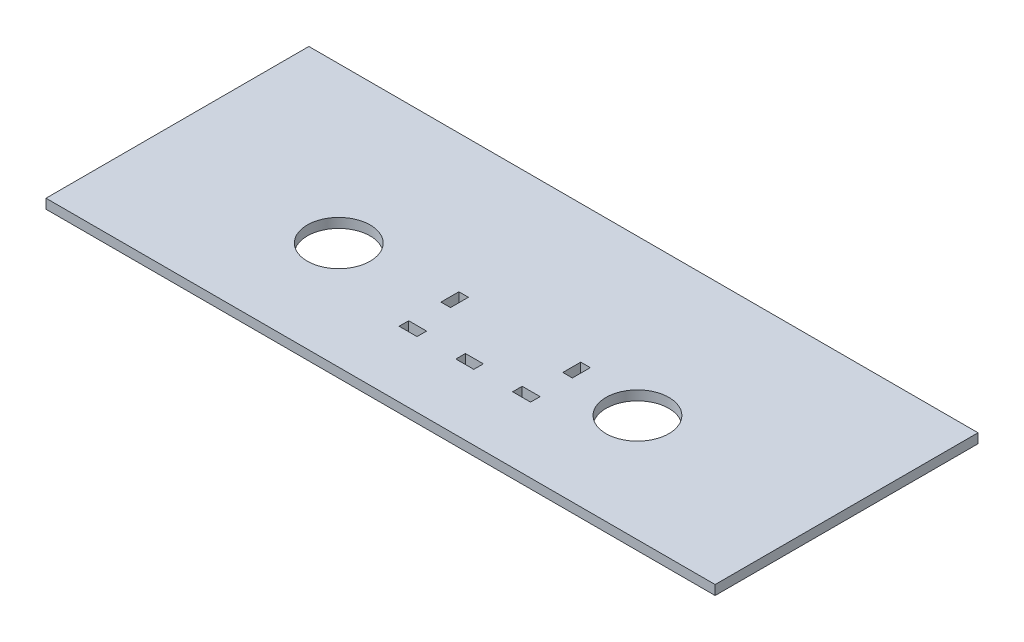
SolidWorks part; units mm, degrees
ref_plane "Front" through (0, 0, 0) normal (0, 0, 1) x (1, 0, 0)
ref_plane "Top" through (0, 0, 0) normal (0, 1, 0) x (1, 0, 0)
ref_plane "Right" through (0, 0, 0) normal (1, 0, 0) x (0, 0, -1)
sketch "Sketch1" plane through (0, 0, 0) normal (0, 1, 0) x (1, 0, 0)
  line L1 (177.8, -69.85) -> (-177.8, -69.85)
  line L2 (177.8, -69.85) -> (177.8, 69.85)
  line L3 (177.8, 69.85) -> (-177.8, 69.85)
  line L4 (-177.8, -69.85) -> (-177.8, 69.85)
  line L5 (177.8, -69.85) -> (-177.8, 69.85) construction
  line L6 (177.8, 69.85) -> (-177.8, -69.85) construction
  point P0 (0, 0)
  dimension "D1" = 355.6
  dimension "D2" = 139.7
extrude "Boss-Extrude1" add sketch "Sketch1" along normal blind 5.08
sketch "Sketch2" plane through (0, 5.08, 0) normal (0, 1, 0) x (1, 0, 0)
  line L0 (-79.375, -12.7) -> (79.375, -12.7)
  line L1 (0, -12.7) -> (0, 0)
  line L2 (177.8, 69.85) -> (-177.8, 69.85) construction
  circle A0 centre (-79.375, -12.7) radius 16.7005
  circle A1 centre (79.375, -12.7) radius 16.7005
  dimension "D2" = 33.401
  dimension "D1" = 158.75
  dimension "D3" = 82.55
extrude "Cut-Extrude1" cut sketch "Sketch2" against normal through all
sketch "Sketch4" plane through (0, 5.08, 0) normal (0, 1, 0) x (1, 0, 0)
  line L1 (-25.0444, -3.2004) -> (-19.9644, -3.2004)
  line L2 (-25.0444, -3.2004) -> (-25.0444, -12.7254)
  line L3 (-25.0444, -12.7254) -> (-19.9644, -12.7254)
  line L4 (-19.9644, -3.2004) -> (-19.9644, -12.7254)
  line L5 (-25.0444, -29.8704) -> (-15.5194, -29.8704)
  line L6 (-25.0444, -29.8704) -> (-25.0444, -34.9504)
  line L7 (-25.0444, -34.9504) -> (-15.5194, -34.9504)
  line L8 (-15.5194, -29.8704) -> (-15.5194, -34.9504)
  line L9 (5.1181, -29.8704) -> (14.6431, -29.8704)
  line L10 (5.1181, -29.8704) -> (5.1181, -34.9504)
  line L11 (5.1181, -34.9504) -> (14.6431, -34.9504)
  line L12 (14.6431, -29.8704) -> (14.6431, -34.9504)
  line L13 (35.2806, -29.8704) -> (44.8056, -29.8704)
  line L14 (35.2806, -29.8704) -> (35.2806, -34.9504)
  line L15 (35.2806, -34.9504) -> (44.8056, -34.9504)
  line L16 (44.8056, -29.8704) -> (44.8056, -34.9504)
  line L17 (44.8056, -3.2004) -> (39.7256, -3.2004)
  line L18 (44.8056, -3.2004) -> (44.8056, -12.7254)
  line L19 (44.8056, -12.7254) -> (39.7256, -12.7254)
  line L20 (39.7256, -3.2004) -> (39.7256, -12.7254)
  line L22 (177.8, -69.85) -> (177.8, 69.85) construction
  line L23 (177.8, 69.85) -> (-177.8, 69.85) construction
  point P21 (0.072, 49.2093)
  point P22 (-15.5194, -32.4104)
  dimension "D1" = 5.08
  dimension "D2" = 9.525
  dimension "D3" = 69.85
  dimension "D4" = 31.75
  dimension "D5" = 20.6375
  dimension "D6" = 132.9944
  dimension "D7" = 73.0504
extrude "Cut-Extrude3" cut sketch "Sketch4" against normal through all
